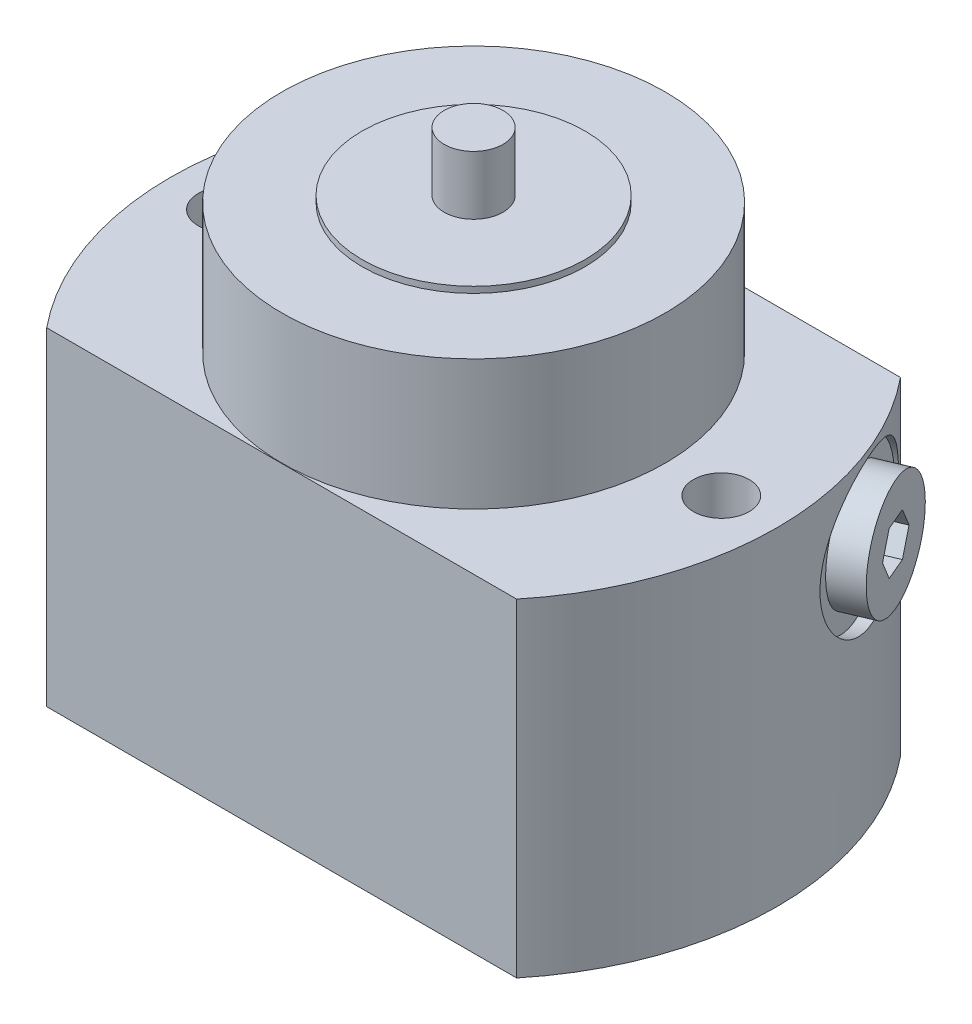
SolidWorks part; units mm, degrees
material "Alloy Steel"
ref_plane "Front Plane" through (0, 0, 0) normal (0, 0, 1) x (1, 0, 0)
ref_plane "Top Plane" through (0, 0, 0) normal (0, 1, 0) x (1, 0, 0)
ref_plane "Right Plane" through (0, 0, 0) normal (1, 0, 0) x (0, 0, -1)
sketch "Sketch1" plane through (0, 0, 0) normal (0, 1, 0) x (1, 0, 0)
  line L0 (-37.9473, 31) -> (37.9473, 31)
  line L1 (0, 0) -> (70.7148, 0) construction
  line L2 (-37.9473, -31) -> (37.9473, -31)
  arc A0 (-37.9473, 31) -> (-37.9473, -31) centre (0, 0) ccw
  arc A1 (37.9473, -31) -> (37.9473, 31) centre (0, 0) ccw
  dimension "D1" = 49
  dimension "D2" = 62
extrude "Extrude1" add sketch "Sketch1" along normal blind 53
sketch "Sketch2" plane through (0, 0, 0) normal (0, 0, 1) x (1, 0, 0)
  line L0 (0, 0) -> (0, 90.1953) construction
  line L1 (0, 84.5) -> (-4.75, 84.5)
  line L2 (-4.75, 84.5) -> (-4.75, 75)
  line L3 (-4.75, 75) -> (-18, 75)
  line L4 (-18, 75) -> (-18, 74)
  line L5 (-18, 74) -> (-30.95, 74)
  line L6 (-30.95, 74) -> (-30.95, 53)
  line L7 (-37.9473, 53) -> (37.9473, 53) construction
  line L8 (-30.95, 53) -> (0, 53)
  line L9 (0, 53) -> (0, 84.5)
  line L10 (-37.9473, 0) -> (37.9473, 0) construction
  dimension "D1" = 9.5
  dimension "D2" = 9.5
  dimension "D3" = 75
  dimension "D4" = 1
  dimension "D5" = 36
  dimension "D6" = 61.9
revolve "Revolve1" add sketch "Sketch2" angle 360 about L0
hole_wizard "Hole1" positions "Sketch4" profile "Sketch3" legacy end condition up to next
sketch "Sketch4" plane through (0, 53, 0) normal (0, 1, 0) x (-1, 0, 0)
  line L0 (0, 0) -> (0, 47.5777) construction
  point P0 (40, 0)
  point P7 (-40, 0)
  dimension "D1" = 80
sketch "Sketch3" plane through (-40, 53, 0) normal (1, 0, 0) x (0, 0, 1)
  line L0 (0, 0) -> (0, 53)
  line L1 (0, 53) -> (4.5, 53)
  line L2 (4.5, 53) -> (4.5, 0)
  line L3 (4.5, 0) -> (0, 0)
  line L4 (0, 110) -> (0, -10) construction
  dimension "Diameter" = 9
  dimension "Depth" = 53
sketch "Sketch5" plane through (0, 0, 0) normal (0, -1, 0) x (1, 0, 0)
  circle A0 centre (0, 0) radius 4
  dimension "D1" = 8
extrude "Cut-Extrude1" cut sketch "Sketch5" against normal blind 4
sketch "Sketch6" plane through (0, 0, 0) normal (0, -1, 0) x (1, 0, 0)
  circle A0 centre (31, -13) radius 5.5
  dimension "D3" = 11
  dimension "D1" = 31
  dimension "D2" = 13
extrude "Cut-Extrude2" cut sketch "Sketch6" against normal blind 3
sketch "Sketch7" plane through (0, 3, 0) normal (0, -1, 0) x (1, 0, 0)
  circle A0 centre (31, -13) radius 2
  dimension "D1" = 4
extrude "Cut-Extrude3" cut sketch "Sketch7" against normal blind 33
ref_plane "Plane1" through (0, 0, 0) normal (0.3907, 0, 0.9205) x (0.9205, 0, -0.3907)
sketch "Sketch8" plane through (0, 0, 0) normal (0.3907, 0, 0.9205) x (0.9205, 0, -0.3907)
  line L0 (51.5856, 40) -> (-19.0781, 40) construction
  line L1 (-47.0434, 0) -> (22.818, 0) construction
  line L2 (49, 28) -> (47, 28)
  line L3 (49, 0) -> (49, 53) construction
  line L4 (47, 28) -> (47, 33.4215)
  line L5 (47, 33.4215) -> (45.5174, 34.2775)
  line L6 (45.5174, 34.2775) -> (32, 34.2775)
  line L7 (32, 34.2775) -> (32, 40)
  line L8 (32, 40) -> (49, 40)
  line L9 (49, 40) -> (49, 28)
  dimension "D1" = 40
  dimension "D2" = 2
  dimension "D3" = 15
  dimension "D4" = 11.445
  dimension "D5" = 24
  dimension "D6" = 30
  dimension "D7" = 13.157
revolve "Cut-Revolve1" cut sketch "Sketch8" angle 360 about L0
sketch "Sketch9" plane through (0, 0, 0) normal (0.3907, 0, 0.9205) x (0.9205, 0, -0.3907)
  line L0 (58.5879, 40) -> (15.4121, 40) construction
  line L1 (32, 40) -> (45.5174, 40) construction
  line L2 (47, 28) -> (47, 52) construction
  line L3 (35.6098, 34.2775) -> (45.5174, 34.2775) construction
  line L4 (47, 31) -> (47, 34.2775)
  line L5 (38, 34.2775) -> (47, 34.2775)
  line L6 (47, 31) -> (52, 31)
  line L7 (52, 31) -> (52, 40)
  line L8 (52, 40) -> (37, 40)
  line L9 (37, 40) -> (37, 35.2775)
  line L10 (37, 35.2775) -> (38, 34.2775)
  dimension "D1" = 45
  dimension "D2" = 4.7225
  dimension "D3" = 10
  dimension "D4" = 5
  dimension "D5" = 18
revolve "Revolve2" add sketch "Sketch9" angle 360 about L0
sketch "Sketch10" plane through (47.8663, 0, -20.318) normal (0.9205, 0, -0.3907) x (-0.3907, 0, -0.9205)
  line L1 (4.0415, 40) -> (2.0207, 43.5)
  line L2 (2.0207, 43.5) -> (-2.0207, 43.5)
  line L3 (-2.0207, 43.5) -> (-4.0415, 40)
  line L4 (-4.0415, 40) -> (-2.0207, 36.5)
  line L5 (-2.0207, 36.5) -> (2.0207, 36.5)
  line L6 (2.0207, 36.5) -> (4.0415, 40)
  circle A0 centre (0, 40) radius 3.5 construction
  circle A1 centre (0, 40) radius 9 construction
  dimension "D1" = 7
extrude "Cut-Extrude4" cut sketch "Sketch10" against normal blind 5
